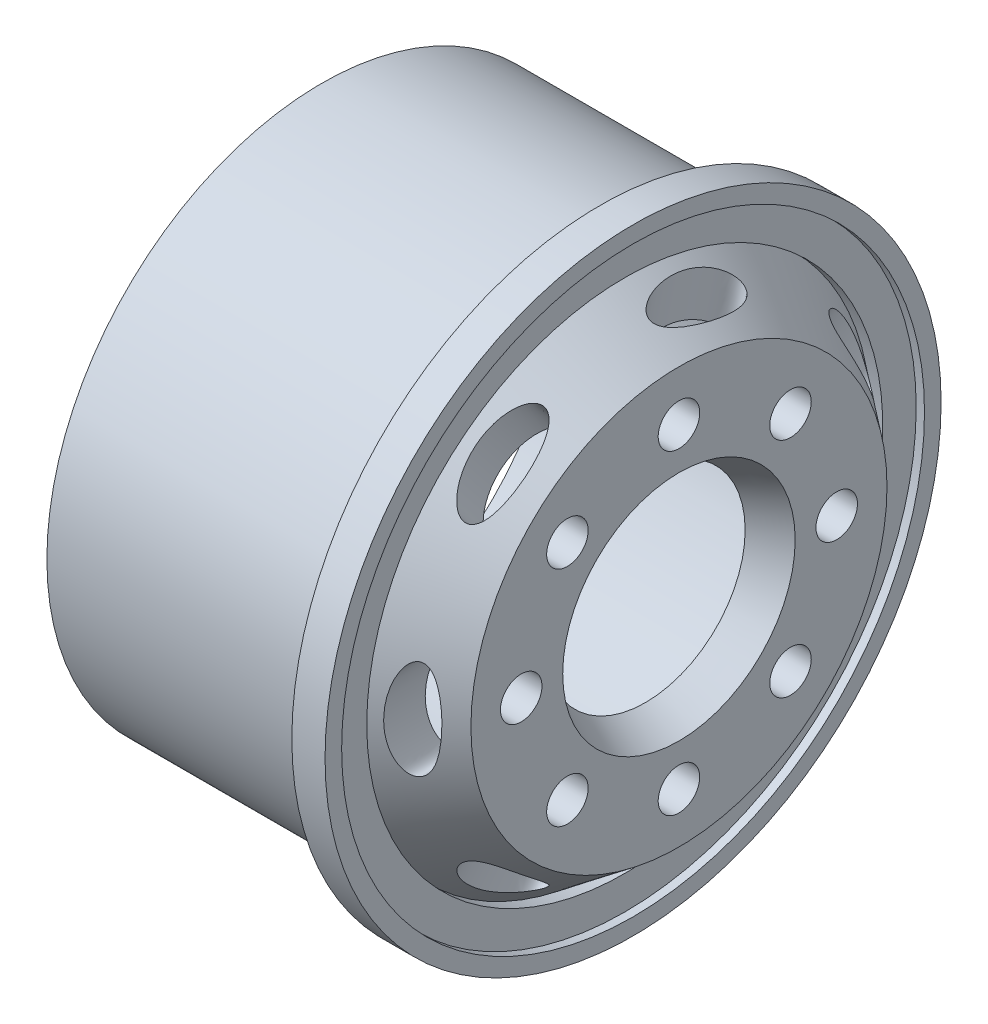
SolidWorks part; units mm, degrees
ref_plane "Front Plane" through (0, 0, 0) normal (0, 0, 1) x (1, 0, 0)
ref_plane "Top Plane" through (0, 0, 0) normal (0, 1, 0) x (1, 0, 0)
ref_plane "Right Plane" through (0, 0, 0) normal (1, 0, 0) x (0, 0, -1)
sketch "Sketch1" plane through (0, 0, 0) normal (0, 1, 0) x (1, 0, 0)
  line L0 (-37.2789, 0) -> (44.8184, 0) construction
  line L12 (-12.5637, 14.55) -> (-12.5637, 16.55)
  line L13 (-12.5637, 16.55) -> (4.1863, 16.55)
  line L18 (5.6863, 15.538) -> (4.9553, 15.538)
  line L23 (4.9553, 15.538) -> (8.9491, 12.5285)
  line L26 (-12.5637, 14.55) -> (2.9431, 14.55)
  line L27 (2.9431, 14.55) -> (6.9363, 11.5409)
  line L28 (4.1863, 16.55) -> (4.1863, 18.55)
  line L29 (4.1863, 18.55) -> (5.6863, 18.55)
  line L30 (5.6863, 17.55) -> (5.6863, 15.538)
  line L34 (6.9363, 11.5409) -> (6.9363, 6)
  line L37 (8.9491, 12.5285) -> (8.9491, 7)
  line L38 (6.9363, 6) -> (8.9491, 7)
  line L39 (5.6863, 18.55) -> (6.1863, 18.55)
  line L40 (6.1863, 18.55) -> (6.1863, 17.55)
  line L41 (6.1863, 17.55) -> (5.6863, 17.55)
  point P3 (8.936, 7.0891)
  point P4 (7.9363, 16.8502)
  point P5 (4.0798, 13.7427)
  point P16 (8.0798, 11.847)
  dimension "D1" = 29.1
  dimension "D2" = 12
  dimension "D4" = 2
  dimension "D5" = 2
  dimension "D6" = 1.5
  dimension "D7" = 143
  dimension "D8" = 3.9932
  dimension "D9" = 19.5
  dimension "D10" = 1
  dimension "D11" = 0.5
  dimension "D12" = 33.1
  dimension "D3" = 5
  dimension "D15" = 19.5
  dimension "D19" = 23.0818
revolve "Revolve1" add sketch "Sketch1" angle 360 about L0
sketch "Sketch2" plane through (8.9491, 0, 0) normal (1, 0, 0) x (0, 0, -1)
  circle A0 centre (0, 0) radius 9.5 construction
  circle A1 centre (0, 9.5) radius 1.25
  circle A2 centre (6.7175, 6.7175) radius 1.25
  circle A3 centre (9.5, 0) radius 1.25
  circle A4 centre (6.7175, -6.7175) radius 1.25
  circle A5 centre (0, -9.5) radius 1.25
  circle A6 centre (-6.7175, -6.7175) radius 1.25
  circle A7 centre (-9.5, 0) radius 1.25
  circle A8 centre (-6.7175, 6.7175) radius 1.25
  point P22 (0, 0)
  dimension "D1" = 19
  dimension "D2" = 2.5
  dimension "D3" = 8
extrude "Cut-Extrude1" cut sketch "Sketch2" against normal through all
ref_plane "Plane1" through (0, 0, 15) normal (0, 0, 1) x (1, 0, 0)
sketch "Sketch3" plane through (0, 0, 15) normal (0, 0, 1) x (1, 0, 0)
  line L0 (6.9522, 14.0332) -> (6.9522, -14.0332) construction
  line L1 (8.9491, 12.5285) -> (4.9553, 15.538) construction
  line L2 (4.9553, -15.538) -> (8.9491, -12.5285) construction
  ellipse E0 centre (6.9522, 0) end of major axis (6.9522, -3) minor radius 1
  dimension "D1" = 2
  dimension "D2" = 6
extrude "Cut-Extrude2" cut sketch "Sketch3" against normal up to surface (3.8682 mm away)
pattern_circular "CirPattern1" count 7 over 360 about axis through (8.9491, 0, 0) along (-1, 0, 0) of "Cut-Extrude2"
